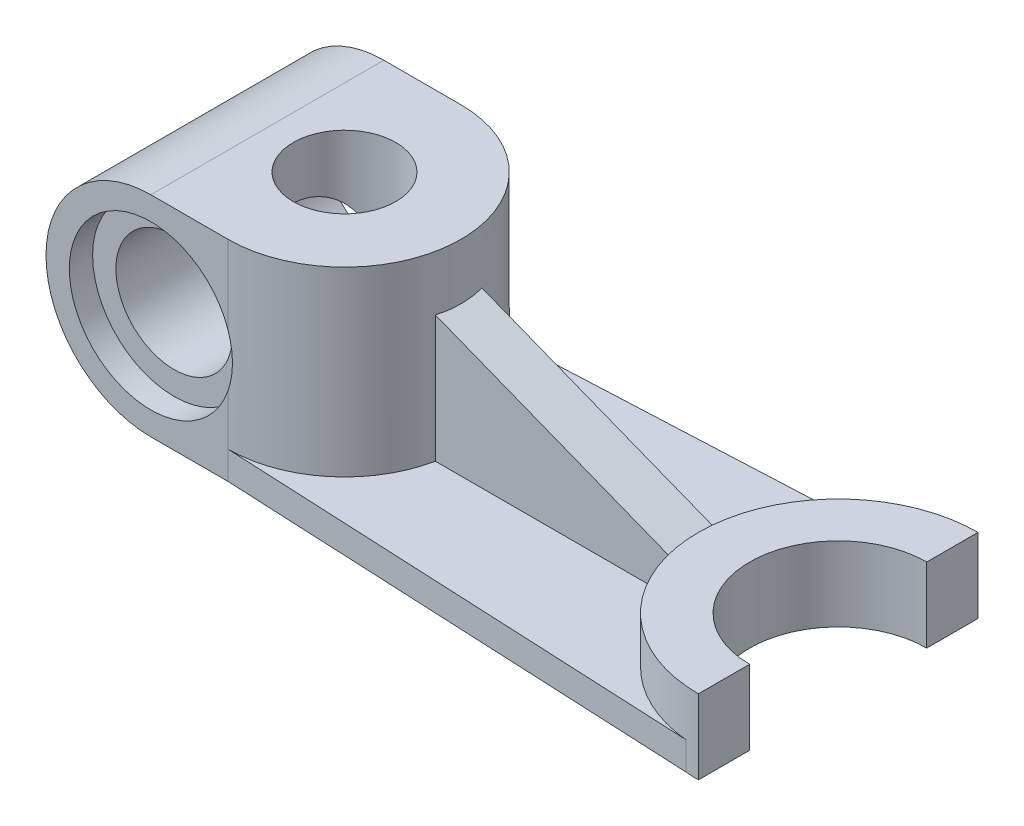
SolidWorks part; units mm, degrees
material "Alloy Steel"
ref_plane "Front Plane" through (0, 0, 0) normal (0, 0, 1) x (1, 0, 0)
ref_plane "Top Plane" through (0, 0, 0) normal (0, 1, 0) x (1, 0, 0)
ref_plane "Right Plane" through (0, 0, 0) normal (1, 0, 0) x (0, 0, -1)
sketch "Sketch2" plane through (0, 0, 0) normal (0, 1, 0) x (1, 0, 0)
  line L0 (0, 39.5594) -> (0, -35.681) construction
  line L1 (0, 30) -> (0, 19)
  line L2 (0, -19) -> (0, -32.5783)
  arc A0 (0, 30) -> (0, -30) centre (0, 0) ccw
  arc A1 (0, 19) -> (0, -19) centre (0, 0) ccw
  dimension "D1" = 60
  dimension "D2" = 38
extrude "Boss-Extrude1" add sketch "Sketch2" along normal blind 16 contours A1 L1 A0 L2
sketch "Sketch3" plane through (0, 0, 0) normal (0, 1, 0) x (1, 0, 0)
  line L0 (0, 0) -> (-145, 0) construction
  dimension "D1" = 145
sketch "Sketch4" plane through (0, 0, 0) normal (0, 1, 0) x (1, 0, 0)
  line L1 (-122.5, 25) -> (-122.5, -25) construction
  line L2 (-122.5, 25) -> (-105.9413, 25)
  line L3 (-122.5, -25) -> (-105.9413, -25)
  arc A0 (-105.9413, 25) -> (-105.9413, -25) centre (-105.9413, 0) cw
  circle A1 centre (-105.9413, 0) radius 11
  dimension "D1" = 22
  dimension "D2" = 22.5
extrude "Boss-Extrude5" add sketch "Sketch4" along normal blind 45 separate body contours L2 L1 L3 A0 A1
sketch "Sketch8" plane through (0, 0, 25) normal (0, 0, 1) x (1, 0, 0)
  line L2 (-122.5, 0) -> (-122.5, 45)
  arc A0 (-122.5, 45) -> (-122.5, 0) centre (-122.5, 22.5) ccw
  circle A1 centre (-122.5, 22.5) radius 12.5
  line M4 (-122.5, 45) -> (-122.5, 0)
  dimension "D1" = 25
extrude "Boss-Extrude8" add sketch "Sketch8" against normal blind 50 contours A1 A0 M4 | L2 A1 | L2 A1
sketch "Sketch11" plane through (0, 0, 25) normal (0, 0, 1) x (1, 0, 0)
  line L0 (-145, 59.4005) -> (-145, -10.375) construction
  circle A1 centre (-122.5, 22.5) radius 12.5
  dimension "D2" = 25
extrude "Cut-Extrude1" cut sketch "Sketch11" against normal blind 50
sketch "Sketch12" plane through (0, 0, 25) normal (0, 0, 1) x (1, 0, 0)
  circle A0 centre (-122.5, 22.5) radius 17.5
  dimension "D1" = 35
extrude "Cut-Extrude2" cut sketch "Sketch12" against normal blind 5
sketch "Sketch13" plane through (0, 0, 0) normal (0, 1, 0) x (1, 0, 0)
  line L0 (-105.9413, -25) -> (0, -30)
  line L1 (-105.9413, 25) -> (0, 30)
  arc A0 (-105.9413, -25) -> (-105.9413, 25) centre (-105.9413, 0) ccw construction
  arc A1 (0, 30) -> (0, -30) centre (0, 0) ccw construction
  arc A2 (-105.9413, -25) -> (-105.9413, 25) centre (-105.9413, 0) ccw
  arc A3 (0, 30) -> (0, -30) centre (0, 0) ccw
extrude "Boss-Extrude9" add sketch "Sketch13" along normal blind 6 contours A3 L1 A2 L0
sketch3d "3DSketch1"
  arc A0 (-105.9413, 45, -25) -> (-105.9413, 45, 25) centre (-105.9413, 45, 0) ccw construction
  arc A1 (0, 16, -30) -> (0, 16, 30) centre (0, 16, 0) ccw construction
  arc A2 (-105.9413, 45, -25) -> (-105.9413, 45, 25) centre (-105.9413, 45, 0) ccw
  arc A3 (0, 16, -30) -> (0, 16, 30) centre (0, 16, 0) ccw
  point P3 (-105.9413, 20, 0)
  point P7 (0, 46, 0)
  point P8 (-105.9413, 20, 0)
  point P9 (0, 46, 0)
sketch "Sketch14" plane through (0, 6, 0) normal (0, 1, 0) x (1, 0, 0)
  line L0 (-80.9413, 0) -> (-30, 0)
  line L1 (-81.4464, 5) -> (-29.5804, 5)
  line L2 (-81.4464, -5) -> (-29.5804, -5)
  line L4 (-29.5804, -5) -> (-30, 0)
  arc A0 (-105.9413, -25) -> (-105.9413, 25) centre (-105.9413, 0) ccw construction
  arc A1 (0, 30) -> (0, -30) centre (0, 0) ccw construction
  dimension "D1" = 5
  dimension "D2" = 5
sketch "Sketch16" plane through (0, 0, 0) normal (0, 0, 1) x (1, 0, 0)
  line L2 (-80.9413, 6) -> (-80.9413, 45) construction
  line L3 (-80.9413, 33) -> (-30, 13)
  line L4 (-30, 16) -> (-30, 6) construction
  line L6 (-105.9413, 45) -> (-80.9413, 45) construction
  dimension "D1" = 12
  dimension "D2" = 3
rib "Rib4" sketch "Sketch16" sketch "Sketch16" thickness 10 extrusion direction parallel to sketch draft on no parameters "D1"=10
